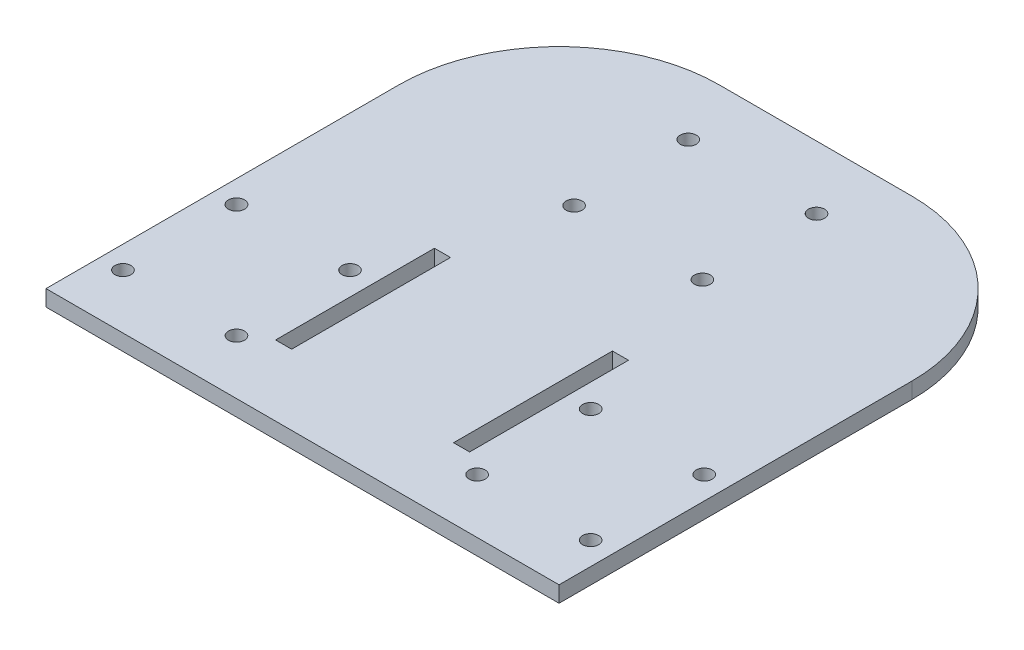
SolidWorks part; units mm, degrees
material "Acrylic (Medium-high impact)"
ref_plane "Front Plane" through (0, 0, 0) normal (0, 0, 1) x (1, 0, 0)
ref_plane "Top Plane" through (0, 0, 0) normal (0, 1, 0) x (1, 0, 0)
ref_plane "Right Plane" through (0, 0, 0) normal (1, 0, 0) x (0, 0, -1)
sketch "Sketch1" plane through (0, 0, 0) normal (0, 1, 0) x (1, 0, 0)
  line L1 (-101.6, -101.6) -> (101.6, -101.6)
  line L2 (-101.6, -101.6) -> (-101.6, 101.6)
  line L3 (-101.6, 101.6) -> (101.6, 101.6)
  line L4 (101.6, -101.6) -> (101.6, 101.6)
  line L5 (-101.6, -101.6) -> (101.6, 101.6) construction
  line L6 (-101.6, 101.6) -> (101.6, -101.6) construction
  point P0 (0, 0)
  dimension "D1" = 203.2
  dimension "D2" = 203.2
extrude "Boss-Extrude1" add sketch "Sketch1" along normal blind 6.35
sketch "Sketch2" plane through (0, 6.35, 0) normal (0, 1, 0) x (1, 0, 0)
  line L9 (101.6, 38.1) -> (101.6, 101.6)
  line L10 (101.6, 101.6) -> (38.1, 101.6)
  line L11 (-38.1, 101.6) -> (-101.6, 101.6)
  line L12 (-101.6, 101.6) -> (-101.6, 38.1)
  arc A2 (101.6, 38.1) -> (38.1, 101.6) centre (38.1, 38.1) ccw
  arc A3 (-101.6, 38.1) -> (-38.1, 101.6) centre (-38.1, 38.1) cw
extrude "Cut-Extrude1" cut sketch "Sketch2" against normal through all
sketch "Sketch9" plane through (0, 0, 0) normal (0, -1, 0) x (1, 0, 0)
  line L0 (-38.766, 10.8317) -> (-38.512, 10.8317) construction
  line L1 (-38.766, 73.756) -> (-38.512, 73.756) construction
  line L2 (38.5855, 10.8317) -> (38.3315, 10.8317) construction
  line L3 (-38.512, 10.8317) -> (-32.162, 10.8317)
  line L4 (-38.512, 10.8317) -> (-38.512, 73.756)
  line L5 (-38.512, 73.756) -> (-32.162, 73.756)
  line L6 (-32.162, 10.8317) -> (-32.162, 73.756)
  line L7 (38.5855, 73.756) -> (38.3315, 73.756) construction
  line L8 (-101.6, 101.6) -> (101.6, 101.6) construction
  line L13 (38.3315, 73.756) -> (31.9815, 73.756)
  line L14 (38.3315, 73.756) -> (38.3315, 10.8317)
  line L15 (38.3315, 10.8317) -> (31.9815, 10.8317)
  line L16 (31.9815, 73.756) -> (31.9815, 10.8317)
  line L17 (-101.6, -38.1) -> (-101.6, 101.6) construction
  circle A0 centre (-47.7463, 64.7757) radius 3.175 construction
  circle A1 centre (-47.7463, 19.812) radius 3.175 construction
  circle A2 centre (-92.71, 19.812) radius 3.175 construction
  circle A3 centre (-92.71, 64.7757) radius 3.175 construction
  circle A4 centre (-25.4903, -11.842) radius 3.175 construction
  circle A5 centre (25.3097, -11.842) radius 3.175 construction
  circle A6 centre (25.3097, -57.054) radius 3.175 construction
  circle A7 centre (-25.4903, -57.054) radius 3.175 construction
  circle A8 centre (47.5658, 19.812) radius 3.175 construction
  circle A9 centre (92.5295, 19.812) radius 3.175 construction
  circle A10 centre (92.5295, 64.7757) radius 3.175 construction
  circle A11 centre (47.5658, 64.7757) radius 3.175 construction
  circle A12 centre (-25.4903, -31.4508) radius 3.175
  circle A13 centre (25.3097, -31.4508) radius 3.175
  circle A14 centre (-25.4903, -76.6628) radius 3.175
  circle A15 centre (25.3097, -76.6628) radius 3.175
  circle A16 centre (-47.7463, 80.0157) radius 3.175
  circle A17 centre (-92.71, 80.0157) radius 3.175
  circle A18 centre (-47.7463, 35.052) radius 3.16
  circle A19 centre (-92.71, 35.052) radius 3.2058
  circle A20 centre (47.5658, 80.0157) radius 3.175
  circle A21 centre (92.5295, 80.0157) radius 3.175
  circle A22 centre (47.5658, 35.052) radius 3.175
  circle A23 centre (92.5295, 35.052) radius 3.175
  dimension "D22" = 6.35
  dimension "D23" = 6.35
  dimension "D24" = 6.35
  dimension "D26" = 6.35
  dimension "D27" = 6.35
  dimension "D28" = 6.35
  dimension "D29" = 6.35
  dimension "D30" = 6.35
  dimension "D31" = 6.35
  dimension "D32" = 6.35
  dimension "D33" = 6.35
  dimension "D36" = 19.6088
  dimension "D37" = 19.6088
  dimension "D38" = 19.6088
  dimension "D40" = 15.24
  dimension "D41" = 15.24
  dimension "D44" = 6.35
  dimension "D45" = 6.35
  dimension "D46" = 6.35
  dimension "D47" = 6.35
  dimension "D48" = 6.35
  dimension "D49" = 6.35
  dimension "D50" = 6.4115
  dimension "D51" = 6.32
  dimension "D1" = 0.254
  dimension "D2" = 6.35
  dimension "D4" = 44.9637
  dimension "D5" = 63.5883
  dimension "D6" = 44.9637
  dimension "D7" = 54.6863
  dimension "D8" = 53.944
  dimension "D9" = 60.548
  dimension "D10" = 135.86
  dimension "D11" = 141.9453
  dimension "D12" = 125.0145
  dimension "D13" = 131.2955
  dimension "D14" = 140.2758
  dimension "D15" = 185.2395
  dimension "D16" = 190.6185
  dimension "D17" = 122.191
  dimension "D18" = 74.2999
  dimension "D19" = 102.1121
  dimension "D20" = 140.8441
  dimension "D21" = 3.175
  dimension "D25" = 147.3059
  dimension "D34" = 8.89
  dimension "D35" = 81.788
  dimension "D39" = 19.6088
  dimension "D42" = 15.24
  dimension "D43" = 15.24
  dimension "D52" = 15.24
  dimension "D53" = 15.24
  dimension "D54" = 15.24
  dimension "D55" = 15.24
extrude "Cut-Extrude2" cut sketch "Sketch9" against normal through all
